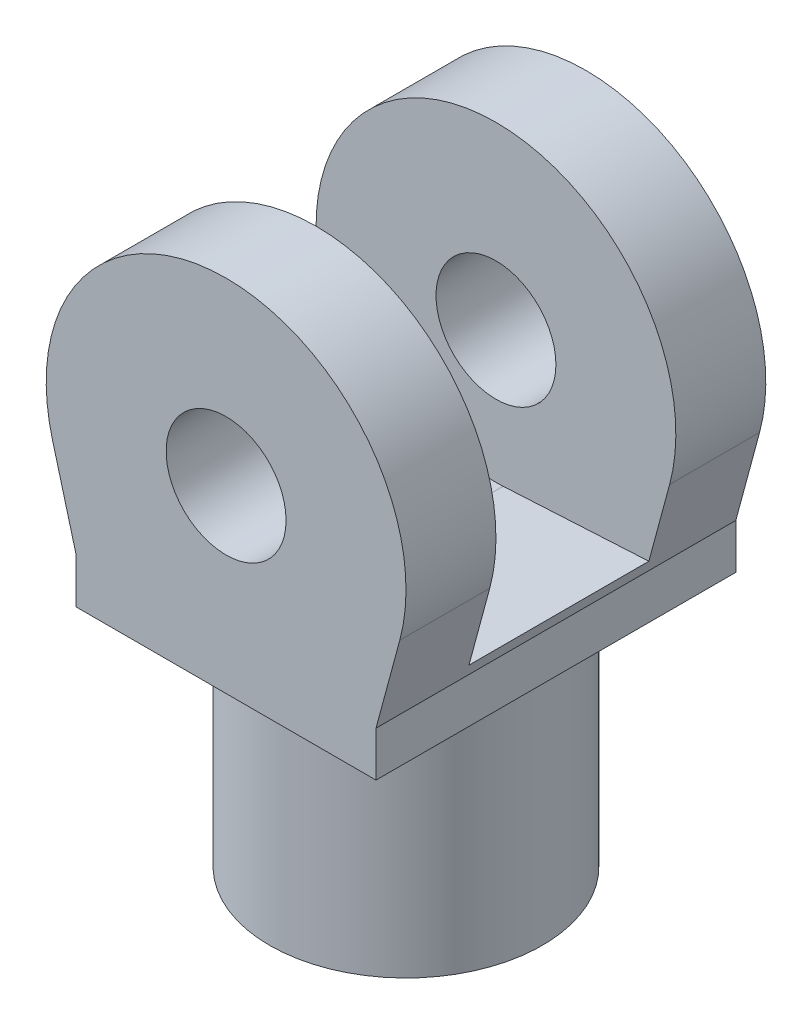
SolidWorks part; units mm, degrees
ref_plane "Front Plane" through (0, 0, 0) normal (0, 0, 1) x (1, 0, 0)
ref_plane "Top Plane" through (0, 0, 0) normal (0, 1, 0) x (1, 0, 0)
ref_plane "Right Plane" through (0, 0, 0) normal (1, 0, 0) x (0, 0, -1)
sketch "Sketch8" plane through (0, 0, 0) normal (0, 1, 0) x (1, 0, 0)
  circle A0 centre (0, 0) radius 2.275
  dimension "D1" = 4.55
extrude "Boss-Extrude4" add sketch "Sketch8" along normal blind 4
sketch "Sketch9" plane through (0, 4, 0) normal (0, 1, 0) x (1, 0, 0)
  line L1 (-2.5, -3) -> (2.5, -3)
  line L2 (-2.5, -3) -> (-2.5, 3)
  line L3 (-2.5, 3) -> (2.5, 3)
  line L4 (2.5, -3) -> (2.5, 3)
  line L5 (-2.5, -3) -> (2.5, 3) construction
  line L6 (-2.5, 3) -> (2.5, -3) construction
  point P0 (0, 0)
  dimension "D1" = 6
  dimension "D2" = 5
extrude "Boss-Extrude5" add sketch "Sketch9" along normal blind 0.75
sketch "Sketch10" plane through (0, 0, 0) normal (0, 0, 1) x (1, 0, 0)
  line L0 (-2.8963, 6.2181) -> (-2.5, 4.75)
  line L1 (-2.5, 4.75) -> (2.5, 4.75)
  line L2 (2.5, 4.75) -> (2.8963, 6.2181)
  line L4 (0, 7) -> (0, 0) construction
  line L5 (-2.275, 0) -> (2.275, 0) construction
  arc A0 (-2.8963, 6.2181) -> (2.8963, 6.2181) centre (0, 7) cw
  circle A1 centre (0, 7) radius 1
  dimension "D1" = 2
  dimension "D3" = 3
  dimension "D2" = 2.25
extrude "Boss-Extrude6" add sketch "Sketch10" along normal mid plane 6
sketch "Sketch11" plane through (0, 0, 0) normal (0, 0, 1) x (1, 0, 0)
  line L0 (-0.1197, 4.8033) -> (-17.5, 5.75)
  line L1 (-17.5, 5.75) -> (-17.5, 11.2343)
  line L2 (-17.5, 11.2343) -> (17.5, 11.2343)
  line L3 (17.5, 5.75) -> (0.1197, 4.8033)
  line L4 (17.5, 11.2343) -> (17.5, 5.75)
  line L5 (0, 7) -> (0, 11.2343) construction
  arc A1 (-0.1197, 4.8033) -> (0.1197, 4.8033) centre (0, 7) ccw
  dimension "D1" = 2.2
  dimension "D2" = 1.25
  dimension "D3" = 35
extrude "Cut-Extrude2" cut sketch "Sketch11" against normal mid plane 3
